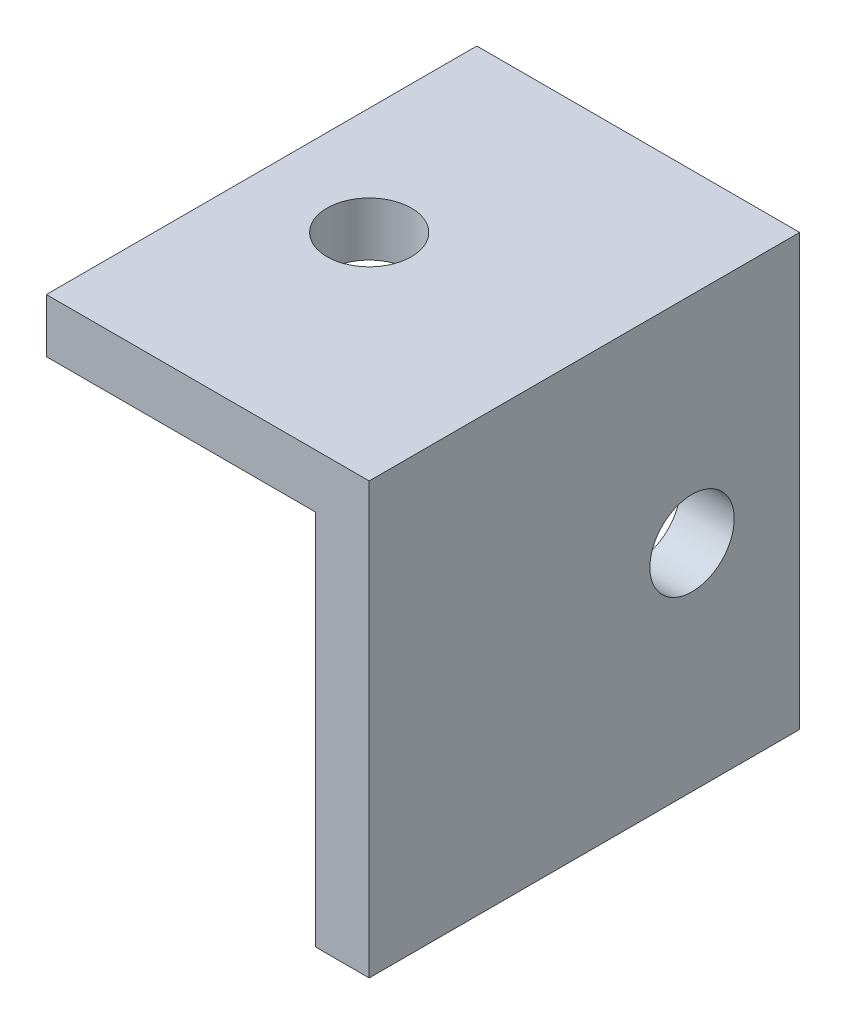
SolidWorks part; units mm, degrees
ref_plane "Front Plane" through (0, 0, 0) normal (0, 0, 1) x (1, 0, 0)
ref_plane "Top Plane" through (0, 0, 0) normal (0, 1, 0) x (1, 0, 0)
ref_plane "Right Plane" through (0, 0, 0) normal (1, 0, 0) x (0, 0, -1)
sketch "Sketch1" plane through (0, 0, 0) normal (0, 0, 1) x (1, 0, 0)
  line L0 (-524.51, 0) -> (-549.91, 0)
  line L2 (-524.51, 0) -> (-524.51, -25.4)
  dimension "D1" = 25.4
extrude "Extrude-Thin1" add sketch "Sketch1" against normal blind 25.4 thin thin type one direction wall 3.175
hole_wizard "#9 (0.196) Diameter Hole1" positions "Sketch2" profile "Sketch3" hole size "#9" standard "ANSI Inch" end condition up to next
sketch "Sketch2" plane through (-527.685, 0, 0) normal (-1, 0, 0) x (0, 0, 1)
  line L1 (-25.4, -25.4) -> (0, -25.4) construction
  line L2 (-25.4, -3.175) -> (-25.4, -25.4) construction
  point P0 (-19.05, -12.7)
  dimension "D1" = 6.35
  dimension "D2" = 12.7
sketch "Sketch3" plane through (-527.685, -12.7, -19.05) normal (0, 1, 0) x (0, 0, 1)
  line L0 (0, 0) -> (0, 3.175)
  line L1 (0, 3.175) -> (2.4892, 3.175)
  line L2 (2.4892, 3.175) -> (2.4892, 0)
  line L5 (2.4892, 0) -> (0, 0)
  line L11 (0, -6.35) -> (0, 107.95) construction
  dimension "Thru Hole Dia." = 4.9784
  dimension "Thru Hole Depth" = 3.175
hole_wizard "#9 (0.196) Diameter Hole3" positions "Sketch7" profile "Sketch8" hole size "#9" standard "ANSI Inch" end condition up to next
sketch "Sketch7" plane through (0, -3.175, 0) normal (0, -1, 0) x (-1, 0, 0)
  line L0 (549.91, 0) -> (527.685, 0) construction
  line L1 (549.91, 25.4) -> (549.91, 0) construction
  point P0 (537.21, 12.7)
  dimension "D1" = 12.7
  dimension "D2" = 12.7
sketch "Sketch8" plane through (-537.21, -3.175, -12.7) normal (1, 0, 0) x (0, 0, -1)
  line L0 (0, 0) -> (0, 3.175)
  line L1 (0, 3.175) -> (2.4892, 3.175)
  line L2 (2.4892, 3.175) -> (2.4892, 0)
  line L5 (2.4892, 0) -> (0, 0)
  line L11 (0, -6.35) -> (0, 107.95) construction
  dimension "Thru Hole Dia." = 4.9784
  dimension "Thru Hole Depth" = 3.175
sketch "Sketch9" plane through (-524.51, 0, 0) normal (1, 0, 0) x (0, 0, -1)
  line L0 (0, 0) -> (609.6, 0) construction
  line L1 (609.6, 0) -> (609.6, -1066.8) construction
  line L2 (609.6, -1066.8) -> (0, 0)
  line L3 (0, -25.4) -> (14.5143, -25.4)
  line L4 (25.4, -25.4) -> (0, -25.4) construction
  line L5 (0, -25.4) -> (0, 0)
  dimension "D1" = 609.6
  dimension "D2" = 1066.8
ref_plane "Plane1" through (0, 0, -12.7) normal (0, 0, 1) x (1, 0, 0)
mirror "Mirror1" [suppressed] about plane through (0, 0, -12.7) normal (0, 0, 1)
sketch "Sketch10" plane through (-524.51, 0, 0) normal (1, 0, 0) x (0, 0, -1)
  circle A0 centre (19.05, -12.7) radius 2.4892 construction
  circle A1 centre (19.05, -12.7) radius 2.4892
extrude "Boss-Extrude1" [suppressed] add sketch "Sketch10" against normal up to surface (3.175 mm away)
sketch "Sketch11" plane through (-549.91, 0, 0) normal (-1, 0, 0) x (0, 0, 1)
  line L4 (0, -3.175) -> (0, 0)
  line L5 (0, 0) -> (-25.4, 0)
  line L6 (-25.4, 0) -> (-25.4, -3.175)
  line L7 (-25.4, -3.175) -> (0, -3.175)
  line L8 (0, -3.175) -> (0, 0)
  line L9 (0, 0) -> (-25.4, 0)
  line L10 (-25.4, 0) -> (-25.4, -3.175)
  line L11 (-25.4, -3.175) -> (0, -3.175)
  dimension "D1" = 0
extrude "Cut-Extrude1" cut sketch "Sketch11" against normal blind 6.35
equation "\"Thick\"= \"in\""
